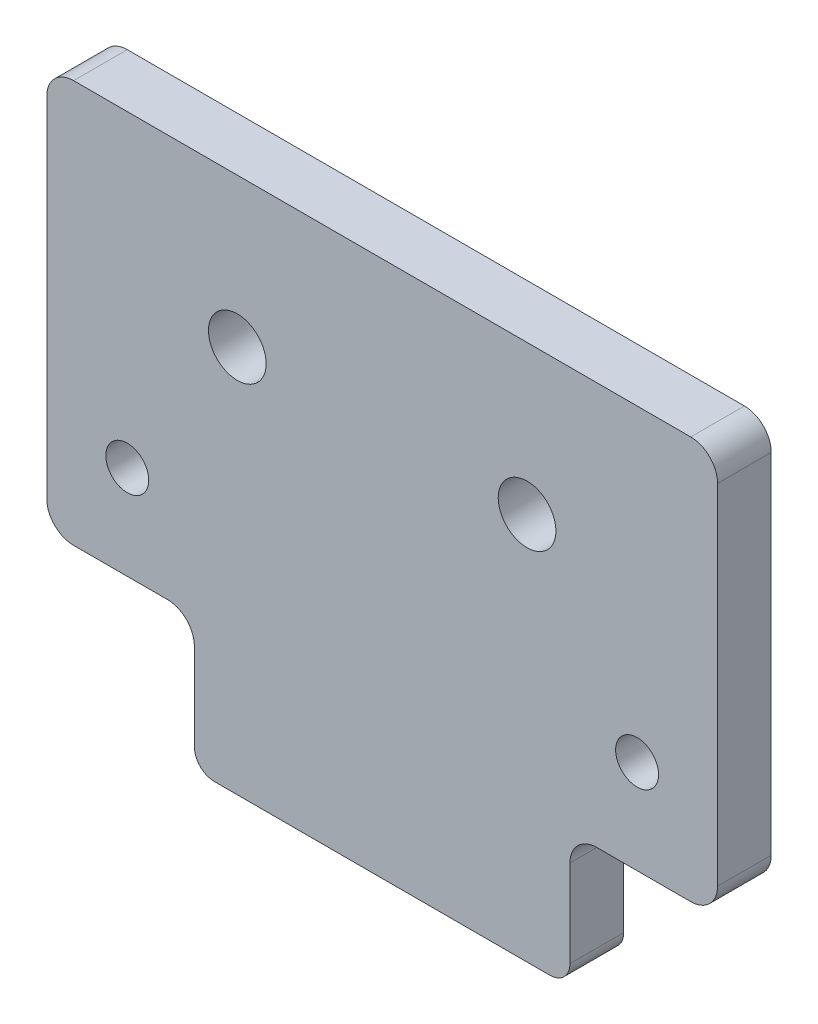
SolidWorks part; units mm, degrees
material "ABS PC"
ref_plane "前视基准面" through (0, 0, 0) normal (0, 0, 1) x (1, 0, 0)
ref_plane "上视基准面" through (0, 0, 0) normal (0, 1, 0) x (1, 0, 0)
ref_plane "右视基准面" through (0, 0, 0) normal (1, 0, 0) x (0, 0, -1)
sketch "草图1" plane through (0, 0, 0) normal (0, 0, 1) x (1, 0, 0)
  line L1 (0, 0) -> (50, 0)
  line L2 (0, 0) -> (0, 30)
  line L3 (0, 30) -> (50, 30)
  line L4 (50, 0) -> (50, 30)
  dimension "D1" = 30
  dimension "D2" = 50
extrude "凸台-拉伸1" add sketch "草图1" along normal blind 4
sketch "草图3" plane through (0, 0, 4) normal (0, 0, 1) x (1, 0, 0)
  line L0 (25, 30) -> (25, -6.9155) construction
  line L1 (50, 30) -> (0, 30) construction
  circle A0 centre (14.2, 18.9) radius 2.15
  circle A1 centre (35.8, 18.9) radius 2.15
  dimension "D3" = 4.3
  dimension "D1" = 21.6
  dimension "D2" = 11.1
extrude "切除-拉伸2" cut sketch "草图3" against normal blind 4
sketch "草图4" plane through (0, 0, 4) normal (0, 0, 1) x (1, 0, 0)
  line L6 (25, 30) -> (25, -41.6889) construction
  line L7 (50, 30) -> (0, 30) construction
  line L8 (0, 0) -> (50, 0) construction
  circle A3 centre (44, 7) radius 1.6
  circle A4 centre (6, 7) radius 1.6
  dimension "D1" = 3.2
  dimension "D2" = 38
  dimension "D3" = 7
extrude "切除-拉伸3" cut sketch "草图4" against normal through all
sketch "草图5" plane through (0, 0, 4) normal (0, 0, 1) x (1, 0, 0)
  line L0 (25, 30) -> (25, -22.9483) construction
  line L1 (50, 30) -> (0, 30) construction
  line L2 (0, 0) -> (50, 0) construction
  line L3 (39, 0) -> (11, 0)
  line L4 (39, 0) -> (39, -10)
  line L5 (39, -10) -> (11, -10)
  line L6 (11, 0) -> (11, -10)
  dimension "D1" = 28
  dimension "D2" = 10
extrude "凸台-拉伸2" add sketch "草图5" against normal up to surface (4 mm away) up to face at (45.6, 7, 0)
fillet "圆角1" radius 1.5 2 edges at (11, -10, 2) (39, -10, 2)
fillet "圆角2" radius 2 6 edges at (50, 0, 2) (50, 30, 2) (0, 30, 2) (0, 0, 2) (11, 0, 2) (39, 0, 2)
